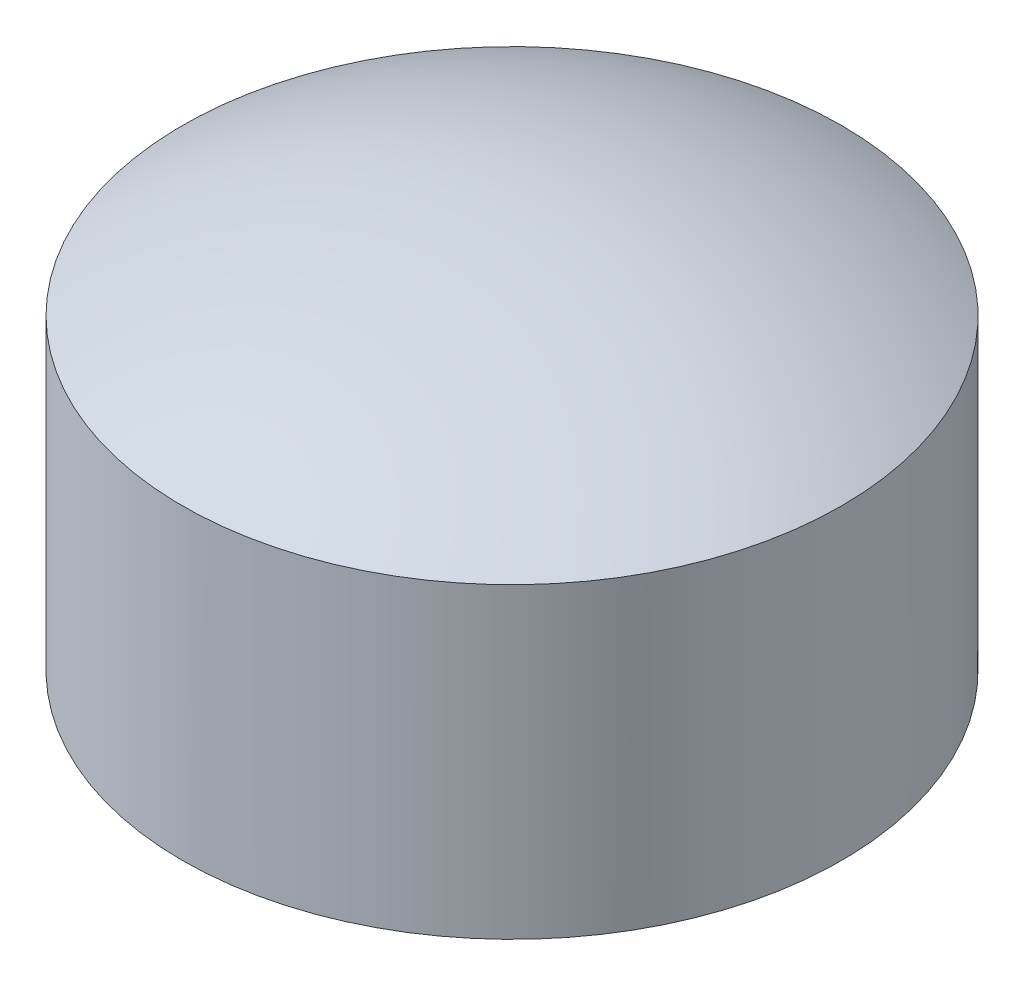
SolidWorks part; units mm, degrees
ref_plane "Front Plane" through (0, 0, 0) normal (0, 0, 1) x (1, 0, 0)
ref_plane "Top Plane" through (0, 0, 0) normal (0, 1, 0) x (1, 0, 0)
ref_plane "Right Plane" through (0, 0, 0) normal (1, 0, 0) x (0, 0, -1)
sketch "Sketch2" plane through (0, 0, 0) normal (0, 1, 0) x (1, 0, 0)
  circle A0 centre (0, 0) radius 5
  dimension "D1" = 10
extrude "Boss-Extrude1" add sketch "Sketch2" along normal blind 8
sketch "Sketch3" plane through (0, 0, 0) normal (0, 0, 1) x (1, 0, 0)
  line L0 (0, 0) -> (0, 9.7452) construction
  line L1 (5, 8) -> (-5, 8) construction
  line L2 (5, 8) -> (-5, 8)
  line L3 (0, 8) -> (0, 14) construction
  line L4 (0, 24) -> (0, 4)
  circle A0 centre (0, 14) radius 10
  dimension "D2" = 20
  dimension "D1" = 6
revolve "Revolve1" add sketch "Sketch3" angle 360 about L4
sketch "Sketch4" plane through (0, 0, 0) normal (0, -1, 0) x (1, 0, 0)
  circle A0 centre (0, 0) radius 5
  circle A1 centre (0, 0) radius 23.7026
  circle A2 centre (0, 0) radius 5
  circle A3 centre (0, 0) radius 5
  circle M3 centre (0, 0) radius 5
  dimension "D1" = 0
extrude "Cut-Extrude1" cut sketch "Sketch4" against normal blind 28 contours A1 M3
sketch "Sketch5" plane through (0, 0, 0) normal (0, -1, 0) x (1, 0, 0)
  circle A0 centre (0, 0) radius 5
extrude "Cut-Extrude2" cut sketch "Sketch5" against normal blind 18
